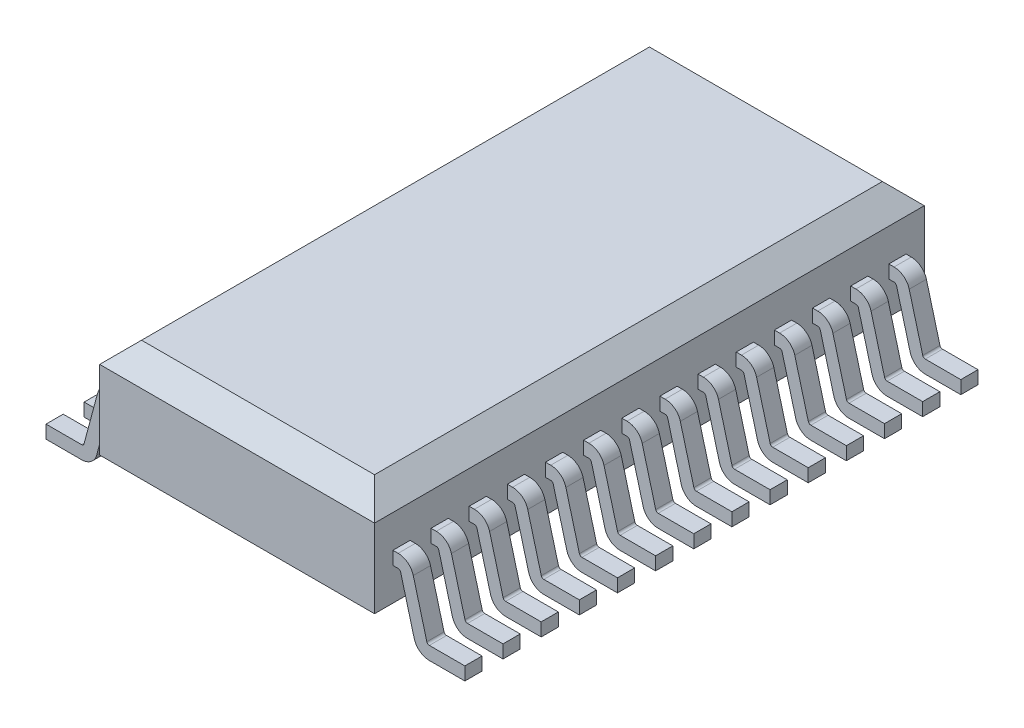
SolidWorks part; units mm, degrees
ref_plane "Front" through (0, 0, 0) normal (0, 0, 1) x (1, 0, 0)
ref_plane "Top" through (0, 0, 0) normal (0, 1, 0) x (1, 0, 0)
ref_plane "Right" through (0, 0, 0) normal (1, 0, 0) x (0, 0, -1)
sketch "Sketch1" plane through (0, 0, 0) normal (0, 0, 1) x (1, 0, 0)
  line L0 (-2.625, -1.15) -> (2.625, -1.15)
  line L2 (2.625, -1.15) -> (2.625, 1.15)
  line L4 (2.625, 1.15) -> (-2.625, 1.15)
  line L6 (-2.625, 1.15) -> (-2.625, -1.15)
  line L8 (0, 2.181) -> (0, 0) construction
  line L9 (0, 0) -> (2.1582, 0) construction
  dimension "D1" = 2.3
  dimension "D2" = 5.25
extrude "Boss-Extrude1" add sketch "Sketch1" along normal mid plane 10.5
chamfer "Chamfer1" distance 0.4 8 edges at (-2.625, -1.15, 0) (0, -1.15, 5.25) (2.625, -1.15, 0) (0, -1.15, -5.25) (2.625, 1.15, 0) (0, 1.15, 5.25) (-2.625, 1.15, 0) (0, 1.15, -5.25)
sketch "Sketch2" plane through (-2.625, 0, 0) normal (-1, 0, 0) x (0, 0, 1)
  line L0 (0, 1.0018) -> (0, 0) construction
  line L1 (-4.9, 0.15) -> (-4.5714, 0.15)
  line L2 (-4.9, 0.15) -> (-4.9, -0.15)
  line L3 (-4.9, -0.15) -> (-4.5714, -0.15)
  line L4 (-4.5714, 0.15) -> (-4.5714, -0.15)
  line L5 (0, 0) -> (1.0818, 0) construction
  line L6 (-4.1714, -0.15) -> (-3.8429, -0.15)
  line L7 (-3.8429, 0.15) -> (-3.8429, -0.15)
  line L8 (-4.1714, 0.15) -> (-3.8429, 0.15)
  line L9 (-4.1714, 0.15) -> (-4.1714, -0.15)
  line L10 (-3.4429, -0.15) -> (-3.1143, -0.15)
  line L11 (-3.1143, 0.15) -> (-3.1143, -0.15)
  line L12 (-3.4429, 0.15) -> (-3.1143, 0.15)
  line L13 (-3.4429, 0.15) -> (-3.4429, -0.15)
  line L14 (-2.7143, -0.15) -> (-2.3857, -0.15)
  line L15 (-2.3857, 0.15) -> (-2.3857, -0.15)
  line L16 (-2.7143, 0.15) -> (-2.3857, 0.15)
  line L17 (-2.7143, 0.15) -> (-2.7143, -0.15)
  line L18 (-1.9857, -0.15) -> (-1.6571, -0.15)
  line L19 (-1.6571, 0.15) -> (-1.6571, -0.15)
  line L20 (-1.9857, 0.15) -> (-1.6571, 0.15)
  line L21 (-1.9857, 0.15) -> (-1.9857, -0.15)
  line L22 (-1.2571, -0.15) -> (-0.9286, -0.15)
  line L23 (-0.9286, 0.15) -> (-0.9286, -0.15)
  line L24 (-1.2571, 0.15) -> (-0.9286, 0.15)
  line L25 (-1.2571, 0.15) -> (-1.2571, -0.15)
  line L26 (-0.5286, -0.15) -> (-0.2, -0.15)
  line L27 (-0.2, 0.15) -> (-0.2, -0.15)
  line L28 (-0.5286, 0.15) -> (-0.2, 0.15)
  line L29 (-0.5286, 0.15) -> (-0.5286, -0.15)
  line L30 (0.2, -0.15) -> (0.5286, -0.15)
  line L31 (0.5286, 0.15) -> (0.5286, -0.15)
  line L32 (0.2, 0.15) -> (0.5286, 0.15)
  line L33 (0.2, 0.15) -> (0.2, -0.15)
  line L34 (0.9286, -0.15) -> (1.2571, -0.15)
  line L35 (1.2571, 0.15) -> (1.2571, -0.15)
  line L36 (0.9286, 0.15) -> (1.2571, 0.15)
  line L37 (0.9286, 0.15) -> (0.9286, -0.15)
  line L38 (1.6571, -0.15) -> (1.9857, -0.15)
  line L39 (1.9857, 0.15) -> (1.9857, -0.15)
  line L40 (1.6571, 0.15) -> (1.9857, 0.15)
  line L41 (1.6571, 0.15) -> (1.6571, -0.15)
  line L42 (2.3857, -0.15) -> (2.7143, -0.15)
  line L43 (2.7143, 0.15) -> (2.7143, -0.15)
  line L44 (2.3857, 0.15) -> (2.7143, 0.15)
  line L45 (2.3857, 0.15) -> (2.3857, -0.15)
  line L46 (3.1143, -0.15) -> (3.4429, -0.15)
  line L47 (3.4429, 0.15) -> (3.4429, -0.15)
  line L48 (3.1143, 0.15) -> (3.4429, 0.15)
  line L49 (3.1143, 0.15) -> (3.1143, -0.15)
  line L50 (3.8429, -0.15) -> (4.1714, -0.15)
  line L51 (4.1714, 0.15) -> (4.1714, -0.15)
  line L52 (3.8429, 0.15) -> (4.1714, 0.15)
  line L53 (3.8429, 0.15) -> (3.8429, -0.15)
  line L54 (4.5714, -0.15) -> (4.9, -0.15)
  line L55 (4.9, 0.15) -> (4.9, -0.15)
  line L56 (4.5714, 0.15) -> (4.9, 0.15)
  line L57 (4.5714, 0.15) -> (4.5714, -0.15)
  dimension "D1" = 0.3
  dimension "D3" = 9.8
  dimension "D4" = 0.4
  dimension "D2" = 14
sketch "Sketch3" plane through (0, 0, 5.25) normal (0, 0, 1) x (1, 0, 0)
  line L0 (-2.625, 0.125) -> (-2.725, 0.125)
  line L1 (-2.625, 0.75) -> (-2.625, -0.75) construction
  line L2 (-3.0148, -0.0974) -> (-3.2735, -1.0629)
  line L3 (-3.3218, -1.1) -> (-4, -1.1)
  line L4 (-4, -1.1) -> (-4, -1.35)
  line L5 (-4, -1.35) -> (-3.3218, -1.35)
  line L6 (-3.032, -1.1276) -> (-2.7733, -0.1621)
  line L7 (-2.725, -0.125) -> (-2.625, -0.125)
  line L8 (-2.625, -0.125) -> (-2.625, 0.125)
  line L9 (0, 0.5259) -> (0, 0) construction
  line L10 (0, 0) -> (1.0172, 0) construction
  line L11 (-2.225, 1.15) -> (2.225, 1.15) construction
  arc A0 (-2.725, 0.125) -> (-3.0148, -0.0974) centre (-2.725, -0.175) ccw
  arc A1 (-3.2735, -1.0629) -> (-3.3218, -1.1) centre (-3.3218, -1.05) cw
  arc A2 (-3.3218, -1.35) -> (-3.032, -1.1276) centre (-3.3218, -1.05) ccw
  arc A3 (-2.7733, -0.1621) -> (-2.725, -0.125) centre (-2.725, -0.175) cw
  point P24 (-2.625, 0)
  dimension "D6" = 0.3
  dimension "D7" = 0.3
  dimension "D1" = 0.25
  dimension "D2" = 8
  dimension "D3" = 2.5
  dimension "D4" = 0.1
  dimension "D5" = 15
extrude "Boss-Extrude2" add sketch "Sketch3" against normal up to vertex (0.6786 mm away) from vertex at -0.35 starting at point (-2.625, -0.15, 4.9)
pattern_linear "LPattern1" count 14 spacing 0.7286 along (0, 0, -1) of "Boss-Extrude2"
mirror "Mirror1" about plane through (0, 0, 0) normal (1, 0, 0) of "LPattern1", "Boss-Extrude2"
